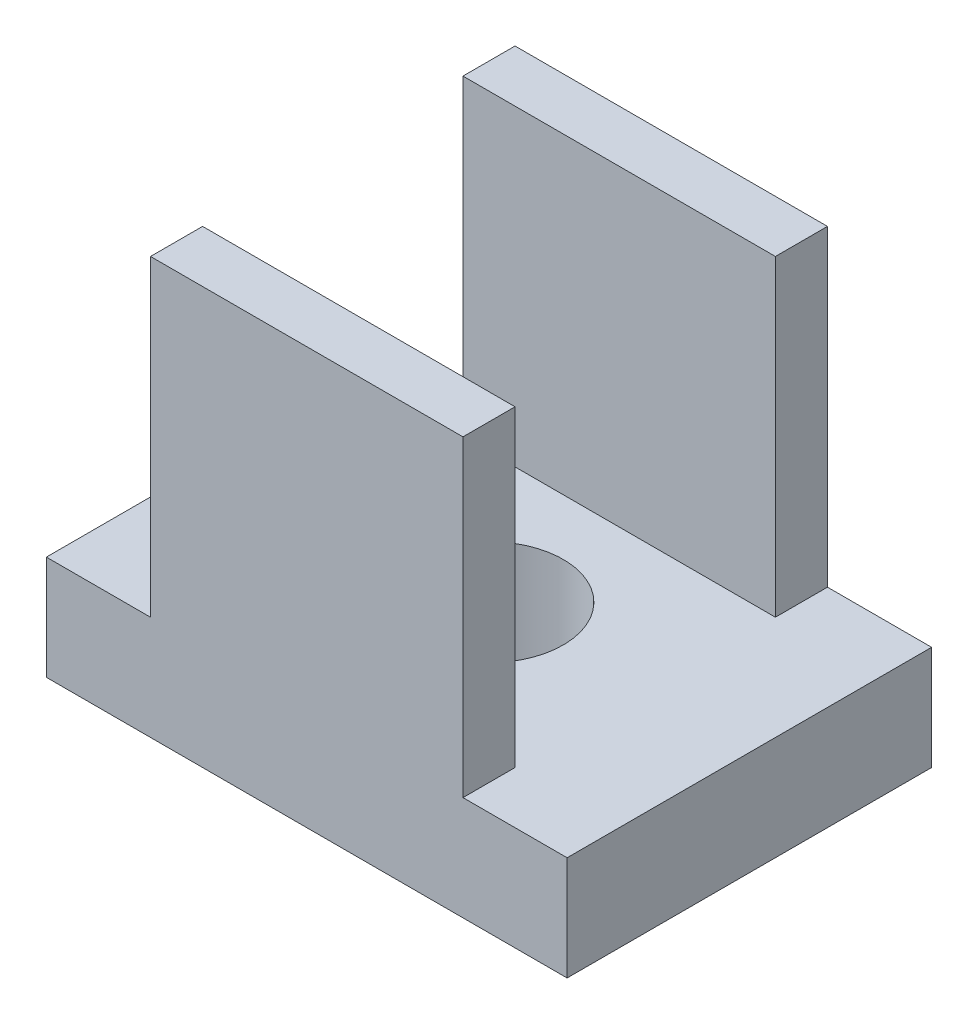
SolidWorks part; units mm, degrees
ref_plane "Front Plane" through (0, 0, 0) normal (0, 0, 1) x (1, 0, 0)
ref_plane "Top Plane" through (0, 0, 0) normal (0, 1, 0) x (1, 0, 0)
ref_plane "Right Plane" through (0, 0, 0) normal (1, 0, 0) x (0, 0, -1)
sketch "Sketch1" plane through (0, 0, 0) normal (0, 1, 0) x (1, 0, 0)
  line L1 (5, -3.5) -> (-5, -3.5)
  line L2 (5, -3.5) -> (5, 3.5)
  line L3 (5, 3.5) -> (-5, 3.5)
  line L4 (-5, -3.5) -> (-5, 3.5)
  line L5 (5, -3.5) -> (-5, 3.5) construction
  line L6 (5, 3.5) -> (-5, -3.5) construction
  point P0 (0, 0)
  dimension "D1" = 10
  dimension "D2" = 7
extrude "Boss-Extrude1" add sketch "Sketch1" along normal blind 2
sketch "Sketch2" plane through (0, 2, 0) normal (0, 1, 0) x (1, 0, 0)
  circle A0 centre (0, 0) radius 1.425
  dimension "D1" = 2.85
extrude "Cut-Extrude1" cut sketch "Sketch2" against normal blind 2
sketch "Sketch3" plane through (0, 2, 0) normal (0, 1, 0) x (1, 0, 0)
  line L0 (0, 0) -> (0, -6.3326) construction
  line L1 (-5, -3.5) -> (5, -3.5) construction
  line L2 (3, -3.5) -> (-3, -3.5)
  line L3 (3, -3.5) -> (3, -2.5)
  line L4 (3, -2.5) -> (-3, -2.5)
  line L5 (-3, -3.5) -> (-3, -2.5)
  dimension "D1" = 1
  dimension "D2" = 6
extrude "Boss-Extrude2" add sketch "Sketch3" along normal blind 6
mirror "Mirror1" about plane through (0, 0, 0) normal (0, 0, 1) of "Boss-Extrude2"
